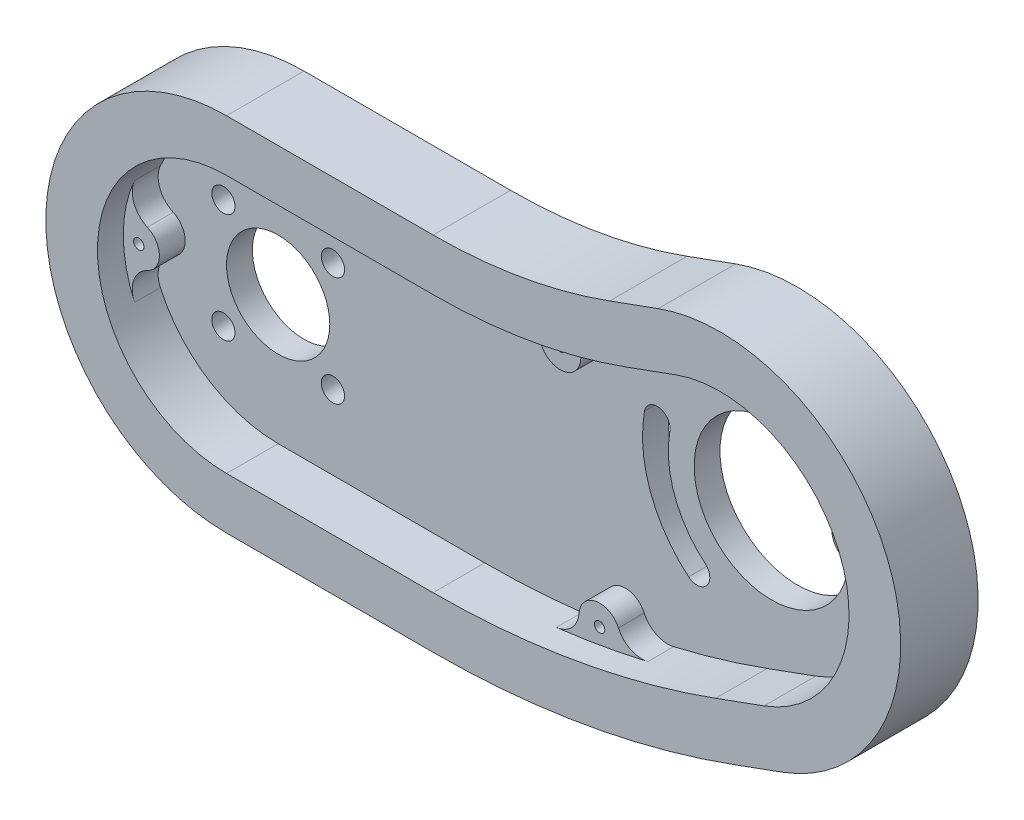
SolidWorks part; units mm, degrees
ref_plane "정면" through (0, 0, 0) normal (0, 0, 1) x (1, 0, 0)
ref_plane "윗면" through (0, 0, 0) normal (0, 1, 0) x (1, 0, 0)
ref_plane "우측면" through (0, 0, 0) normal (1, 0, 0) x (0, 0, -1)
sketch "스케치1" plane through (0, 0, 0) normal (0, 0, 1) x (1, 0, 0)
  line L0 (-1000, 0) -> (49000, 0) construction
  line L1 (0, -990) -> (0, -35) construction
  line L2 (-667.1068, -672.1068) -> (34688.2323, 34683.2323) construction
  line L3 (0, 35) -> (40, 35)
  line L5 (0, -35) -> (40, -35)
  line L8 (40, -955) -> (40, -35) construction
  line L10 (74.202, 41.0307) -> (83.5989, 44.4509)
  line L11 (98.1434, -24.7477) -> (107.5404, -21.3275)
  line L13 (0, 35) -> (0, 48990) construction
  line L14 (40, 35) -> (40, 49045) construction
  line L15 (80.4398, -19.9992) -> (98.1434, -24.7477)
  line L17 (83.5989, 44.4509) -> (107.5404, -21.3275) construction
  arc A0 (0, 35) -> (0, -35) centre (0, 0) ccw
  arc A2 (40, 35) -> (74.202, 41.0307) centre (40, 135) ccw
  arc A3 (40, -35) -> (98.1434, -24.7477) centre (40, 135) ccw
  arc A4 (80.4398, -19.9992) -> (81.5929, -20.5265) centre (95.5696, 11.5617) ccw
  arc A5 (107.5404, -21.3275) -> (83.5989, 44.4509) centre (95.5696, 11.5617) ccw
  dimension "D1" = 100
  dimension "D2" = 70
  dimension "D3" = 40
  dimension "D6" = 170
  dimension "D7" = 70
  dimension "D8" = 35
  dimension "D4" = 10
  dimension "D5" = 70
extrude "보스-돌출1" add sketch "스케치1" along normal blind 20
chamfer "모따기1" distance 10 angle 45 8 edges at (128.4589, 23.5324, 20) (78.9005, 42.7408, 20) (102.8419, -23.0376, 20) (57.3648, 36.5192, 20) (69.5202, -32.4173, 20) (20, 35, 20) (20, -35, 20) (-35, 0, 20)
sketch "스케치2" plane through (0, 0, 20) normal (0, 0, 1) x (1, 0, 0)
  line L8 (94.7232, -15.3508) -> (104.1201, -11.9306)
  line L10 (40, 25) -> (0, 25)
  line L11 (0, -25) -> (40, -25)
  line L14 (40, 25) -> (0, 25)
  line L15 (0, -25) -> (40, -25)
  line L20 (94.7232, -15.3508) -> (104.1201, -11.9306)
  line L22 (87.0191, 35.054) -> (77.6222, 31.6338)
  line L23 (87.0191, 35.054) -> (77.6222, 31.6338)
  arc A8 (104.1201, -11.9306) -> (87.0191, 35.054) centre (95.5696, 11.5617) ccw
  arc A9 (40, 25) -> (77.6222, 31.6338) centre (40, 135) ccw
  arc A10 (0, 25) -> (0, -25) centre (0, 0) ccw
  arc A11 (40, -25) -> (94.7232, -15.3508) centre (40, 135) ccw
  arc A13 (40, 25) -> (77.6222, 31.6338) centre (40, 135) ccw
  arc A14 (0, 25) -> (0, -25) centre (0, 0) ccw
  arc A15 (40, -25) -> (94.7232, -15.3508) centre (40, 135) ccw
  arc A19 (104.1201, -11.9306) -> (87.0191, 35.054) centre (95.5696, 11.5617) ccw
  dimension "D1" = 0
extrude "컷-돌출1" cut sketch "스케치2" against normal blind 15
sketch "스케치3" plane through (0, 0, 5) normal (0, 0, 1) x (1, 0, 0)
  circle A0 centre (95.5696, 11.5617) radius 15
  dimension "D1" = 30
extrude "컷-돌출2" cut sketch "스케치3" against normal blind 20
sketch "스케치4" plane through (0, 0, 5) normal (0, 0, 1) x (1, 0, 0)
  line L0 (0, -967.2447) -> (0, 49032.7553) construction
  line L1 (0, 0) -> (-35355.3391, -35355.3391) construction
  line L2 (-1030, 0) -> (48970, 0) construction
  line L3 (30, -1000.0889) -> (30, 48999.9111) construction
  line L4 (0, 0) -> (-35355.3391, 35355.3391) construction
  circle A0 centre (0, 0) radius 15
  circle A1 centre (-10.6066, 10.6066) radius 2.25
  circle A2 centre (10.6066, 10.6066) radius 2.25
  circle A3 centre (10.6066, -10.6066) radius 2.25
  circle A4 centre (-10.6066, -10.6066) radius 2.25
  circle A8 centre (0, 0) radius 10
  arc A9 (0, 25) -> (0, -25) centre (0, 0) ccw construction
  point P14 (0, 0)
  point P27 (-25, 0)
  dimension "D1" = 4
  dimension "D2" = 30
  dimension "D3" = 45
  dimension "D6" = 4.5
  dimension "D4" = 45
  dimension "D5" = 30
extrude "컷-돌출3" cut sketch "스케치4" against normal blind 20 contours A0 A4 | A0 A4
sketch "스케치5" plane through (0, 0, 5) normal (0, 0, 1) x (1, 0, 0)
  line L0 (221.8926, 57.5395) -> (-32752.1662, -11944.0364) construction
  line L1 (40, -970) -> (40, 49030) construction
  line L2 (70.1902, 52.0531) -> (12071.7661, -32922.0057) construction
  line L3 (-150.1799, 1213.564) -> (7605.1434, -42769.0602) construction
  circle A0 centre (-22, 0) radius 4
  arc A1 (104.1201, -11.9306) -> (87.0191, 35.054) centre (95.5696, 11.5617) ccw construction
  circle A2 centre (116.2429, 19.0861) radius 4
  arc A3 (40, 25) -> (77.6222, 31.6338) centre (40, 135) ccw construction
  arc A4 (40, -25) -> (94.7232, -15.3508) centre (40, 135) ccw construction
  circle A5 centre (59.6222, 23.7167) radius 4
  circle A6 centre (67.2628, -19.6148) radius 4
  arc A7 (0, 25) -> (0, -25) centre (0, 0) ccw construction
  point P13 (119.062, 20.1122)
  point P18 (40, 135)
  point P20 (59.1013, 26.6711)
  point P22 (67.7837, -22.5692)
  point P37 (-25, 0)
  dimension "D1" = 3
  dimension "D2" = 8
  dimension "D4" = 3
  dimension "D7" = 8
  dimension "D8" = 8
  dimension "D3" = 20
  dimension "D5" = 3
  dimension "D6" = 3
extrude "보스-돌출3" add sketch "스케치5" along normal blind 5
fillet "필렛1" radius 5 8 edges at (70.4101, -22.0835, 7.5) (65.1496, -23.0111, 7.5) (117.9494, 22.7039, 7.5) (119.8756, 17.4117, 7.5) (61.6665, 27.1549, 7.5) (56.5254, 26.2484, 7.5) (-24.8409, -2.8159, 7.5) (-24.8409, 2.8159, 7.5)
sketch "스케치6" plane through (0, 0, 10) normal (0, 0, 1) x (1, 0, 0)
  circle A0 centre (59.6222, 23.7167) radius 1
  circle A1 centre (67.2628, -19.6148) radius 1
  circle A2 centre (-22, 0) radius 1
  circle A3 centre (116.2429, 19.0861) radius 1
extrude "컷-돌출4" cut sketch "스케치6" against normal blind 10
fillet "필렛2" radius 5 8 edges at (20, 35, 10) (-35, 0, 10) (20, -35, 10) (69.5202, -32.4173, 10) (102.8419, -23.0376, 10) (128.4589, 23.5324, 10) (78.9005, 42.7408, 10) (57.3648, 36.5192, 10)
sketch "스케치8" plane through (0, 0, 0) normal (0, 0, -1) x (-1, 0, 0)
  line L0 (881.7107, -344.1393) -> (-76.7758, 4.7213) construction
  line L1 (-95.5696, 11.5617) -> (17005.4375, 46996.1927) construction
  line L4 (-95.5696, 11.5617) -> (-47080.2007, 17112.5689) construction
  arc A6 (-79.5, -7.5894) -> (-70.9495, 15.9029) centre (-95.5696, 11.5617) ccw
  arc A7 (-82.7139, -3.7592) -> (-75.8735, 15.0347) centre (-95.5696, 11.5617) ccw
  arc A8 (-70.9495, 15.9029) -> (-75.8735, 15.0347) centre (-73.4115, 15.4688) ccw
  arc A9 (-82.7139, -3.7592) -> (-79.5, -7.5894) centre (-81.1069, -5.6743) ccw
  dimension "D1" = 50
  dimension "D2" = 40
  dimension "D3" = 5
  dimension "D4" = 5
  dimension "D5" = 22.5
  dimension "D6" = 22.5
extrude "컷-돌출5" cut sketch "스케치8" against normal up to next
ref_plane "평면1" through (0, 0, 20) normal (0, 0, -1) x (-1, 0, 0)
sketch "스케치9" plane through (0, 0, 20) normal (0, 0, -1) x (-1, 0, 0)
  line L20 (-107.5404, -21.3275) -> (-98.1434, -24.7477)
  line L21 (-40, -35) -> (0, -35)
  line L22 (0, 35) -> (-40, 35)
  line L23 (-74.202, 41.0307) -> (-83.5989, 44.4509)
  line L24 (-107.5404, -21.3275) -> (-98.1434, -24.7477)
  line L25 (-40, -35) -> (0, -35)
  line L26 (0, 35) -> (-40, 35)
  line L27 (-74.202, 41.0307) -> (-83.5989, 44.4509)
  line L48 (-104.1201, -11.9306) -> (-94.7232, -15.3508)
  line L49 (-77.6222, 31.6338) -> (-87.0191, 35.054)
  line L50 (-40, -25) -> (0, -25)
  line L51 (0, 25) -> (-40, 25)
  line L52 (-104.1201, -11.9306) -> (-94.7232, -15.3508)
  line L53 (-77.6222, 31.6338) -> (-87.0191, 35.054)
  line L54 (-40, -25) -> (0, -25)
  line L55 (0, 25) -> (-40, 25)
  arc A24 (-98.1434, -24.7477) -> (-40, -35) centre (-40, 135) ccw
  arc A25 (0, -35) -> (0, 35) centre (0, 0) ccw
  arc A26 (-74.202, 41.0307) -> (-40, 35) centre (-40, 135) ccw
  arc A27 (-83.5989, 44.4509) -> (-107.5404, -21.3275) centre (-95.5696, 11.5617) ccw
  arc A28 (-98.1434, -24.7477) -> (-40, -35) centre (-40, 135) ccw
  arc A29 (0, -35) -> (0, 35) centre (0, 0) ccw
  arc A30 (-74.202, 41.0307) -> (-40, 35) centre (-40, 135) ccw
  arc A31 (-83.5989, 44.4509) -> (-107.5404, -21.3275) centre (-95.5696, 11.5617) ccw
  arc A69 (-87.0191, 35.054) -> (-104.1201, -11.9306) centre (-95.5696, 11.5617) ccw
  arc A70 (-77.6222, 31.6338) -> (-40, 25) centre (-40, 135) ccw
  arc A71 (-94.7232, -15.3508) -> (-40, -25) centre (-40, 135) ccw
  arc A72 (0, -25) -> (22.8125, -10.2269) centre (0, 0) ccw
  arc A73 (22.8125, -10.2269) -> (22.8125, 10.2269) centre (0, 0) ccw
  arc A74 (22.8125, 10.2269) -> (0, 25) centre (0, 0) ccw
  arc A75 (-87.0191, 35.054) -> (-104.1201, -11.9306) centre (-95.5696, 11.5617) ccw
  arc A76 (-77.6222, 31.6338) -> (-40, 25) centre (-40, 135) ccw
  arc A77 (-94.7232, -15.3508) -> (-40, -25) centre (-40, 135) ccw
  arc A78 (0, -25) -> (22.8125, -10.2269) centre (0, 0) ccw
  arc A79 (22.8125, -10.2269) -> (22.8125, 10.2269) centre (0, 0) ccw
  arc A80 (22.8125, 10.2269) -> (0, 25) centre (0, 0) ccw
  dimension "D1" = 0
  dimension "D2" = 0
extrude "보스-돌출4" add sketch "스케치9" along normal blind 13
sketch "스케치10" plane through (0, 0, 20) normal (0, 0, -1) x (-1, 0, 0)
  line L24 (-74.202, 41.0307) -> (-83.5989, 44.4509)
  line L25 (-107.5404, -21.3275) -> (-98.1434, -24.7477)
  line L26 (-40, -35) -> (0, -35)
  line L27 (0, 35) -> (-40, 35)
  line L28 (-74.202, 41.0307) -> (-83.5989, 44.4509)
  line L29 (-107.5404, -21.3275) -> (-98.1434, -24.7477)
  line L30 (-40, -35) -> (0, -35)
  line L31 (0, 35) -> (-40, 35)
  line L48 (-40, -25) -> (0, -25)
  line L49 (-104.1201, -11.9306) -> (-94.7232, -15.3508)
  line L50 (-77.6222, 31.6338) -> (-87.0191, 35.054)
  line L51 (0, 25) -> (-40, 25)
  line L52 (-40, -25) -> (0, -25)
  line L53 (-104.1201, -11.9306) -> (-94.7232, -15.3508)
  line L54 (-77.6222, 31.6338) -> (-87.0191, 35.054)
  line L55 (0, 25) -> (-40, 25)
  arc A20 (-74.202, 41.0307) -> (-40, 35) centre (-40, 135) ccw
  arc A21 (-83.5989, 44.4509) -> (-107.5404, -21.3275) centre (-95.5696, 11.5617) ccw
  arc A22 (-98.1434, -24.7477) -> (-40, -35) centre (-40, 135) ccw
  arc A23 (0, -35) -> (0, 35) centre (0, 0) ccw
  arc A24 (-74.202, 41.0307) -> (-40, 35) centre (-40, 135) ccw
  arc A25 (-83.5989, 44.4509) -> (-107.5404, -21.3275) centre (-95.5696, 11.5617) ccw
  arc A26 (-98.1434, -24.7477) -> (-40, -35) centre (-40, 135) ccw
  arc A27 (0, -35) -> (0, 35) centre (0, 0) ccw
  arc A48 (-94.7232, -15.3508) -> (-40, -25) centre (-40, 135) ccw
  arc A49 (-87.0191, 35.054) -> (-104.1201, -11.9306) centre (-95.5696, 11.5617) ccw
  arc A50 (-77.6222, 31.6338) -> (-40, 25) centre (-40, 135) ccw
  arc A51 (0, -25) -> (0, 25) centre (0, 0) ccw
  arc A52 (-94.7232, -15.3508) -> (-40, -25) centre (-40, 135) ccw
  arc A53 (-87.0191, 35.054) -> (-104.1201, -11.9306) centre (-95.5696, 11.5617) ccw
  arc A54 (-77.6222, 31.6338) -> (-40, 25) centre (-40, 135) ccw
  arc A55 (0, -25) -> (0, 25) centre (0, 0) ccw
  dimension "D1" = 0
  dimension "D2" = 0
extrude "컷-돌출6" cut sketch "스케치10" along normal blind 5
